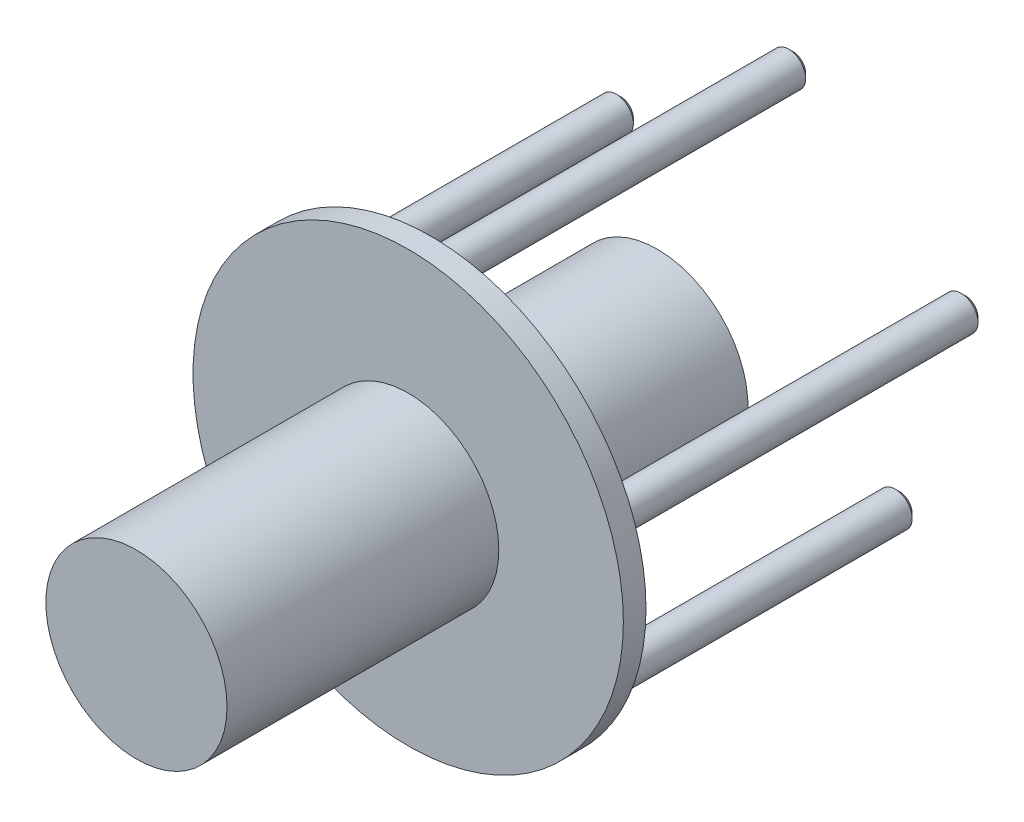
SolidWorks part; units mm, degrees
ref_plane "Front Plane" through (0, 0, 0) normal (0, 0, 1) x (1, 0, 0)
ref_plane "Top Plane" through (0, 0, 0) normal (0, 1, 0) x (1, 0, 0)
ref_plane "Right Plane" through (0, 0, 0) normal (1, 0, 0) x (0, 0, -1)
sketch "Sketch2" plane through (0, 0, 0) normal (0, 0, 1) x (1, 0, 0)
  circle A0 centre (-60.5619, 11.2111) radius 25.4
  circle A1 centre (-12.2483, 26.9092) radius 4.7625
  circle A2 centre (-60.5619, 62.0111) radius 4.7625
  circle A3 centre (-108.8756, 26.9092) radius 4.7625
  circle A4 centre (-90.4214, -29.887) radius 4.7625
  circle A5 centre (-30.7025, -29.887) radius 4.7625
extrude "Boss-Extrude1" add sketch "Sketch2" along normal blind 57.15
sketch "Sketch3" plane through (0, 0, 57.15) normal (0, 0, 1) x (1, 0, 0)
  circle A0 centre (-60.5619, 11.2111) radius 60.325
  dimension "D1" = 120.65
extrude "Boss-Extrude2" add sketch "Sketch3" along normal blind 6.35
sketch "Sketch4" plane through (0, 0, 0) normal (0, 0, -1) x (-1, 0, 0)
  circle A0 centre (60.5619, 11.2111) radius 25.4
extrude "Boss-Extrude3" add sketch "Sketch4" along normal blind 6.35
sketch "Sketch5" plane through (0, 0, 0) normal (0, 0, -1) x (-1, 0, 0)
  circle A0 centre (12.2483, 26.9092) radius 4.7625
  circle A1 centre (30.7025, -29.887) radius 4.7625
  circle A2 centre (90.4214, -29.887) radius 4.7625
  circle A3 centre (108.8756, 26.9092) radius 4.7625
  circle A4 centre (60.5619, 62.0111) radius 4.7625
  point P14 (60.5619, 11.2111)
  dimension "D1" = 5
extrude "Boss-Extrude4" add sketch "Sketch5" along normal blind 44.45
chamfer "Chamfer1" distance 1.27 angle 45 5 edges at (-95.1839, -29.887, -44.45) (-113.6381, 26.9092, -44.45) (-35.465, -29.887, -44.45) (-65.3244, 62.0111, -44.45) (-17.0108, 26.9092, -44.45)
sketch "Sketch7" plane through (0, 0, 63.5) normal (0, 0, 1) x (1, 0, 0)
  circle A0 centre (-60.5619, 11.2111) radius 25.4
  dimension "D1" = 50.8
extrude "Boss-Extrude5" add sketch "Sketch7" along normal blind 76.2
